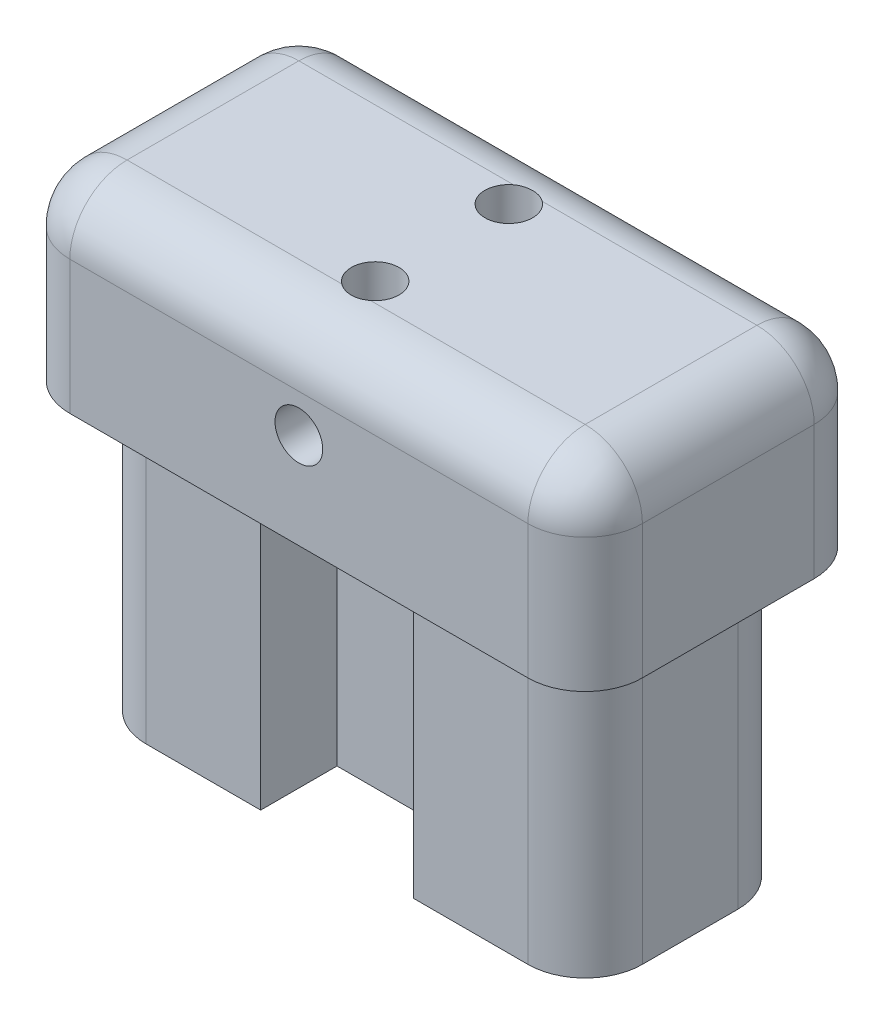
SolidWorks part; units mm, degrees
ref_plane "Front Plane" through (0, 0, 0) normal (0, 0, 1) x (1, 0, 0)
ref_plane "Top Plane" through (0, 0, 0) normal (0, 1, 0) x (1, 0, 0)
ref_plane "Right Plane" through (0, 0, 0) normal (1, 0, 0) x (0, 0, -1)
sketch "Sketch1" plane through (0, 0, 0) normal (0, 1, 0) x (1, 0, 0)
  line L1 (-15, -7.5) -> (15, -7.5)
  line L2 (-15, -7.5) -> (-15, 7.5)
  line L3 (-15, 7.5) -> (15, 7.5)
  line L4 (15, -7.5) -> (15, 7.5)
  line L5 (-15, -7.5) -> (15, 7.5) construction
  line L6 (-15, 7.5) -> (15, -7.5) construction
  point P0 (0, 0)
  dimension "D1" = 30
  dimension "D2" = 15
extrude "Boss-Extrude1" add sketch "Sketch1" along normal blind 10
sketch "Sketch2" plane through (0, 0, 0) normal (0, -1, 0) x (1, 0, 0)
  line L0 (15, 7.5) -> (15, -7.5) construction
  line L1 (-13, -5.5) -> (-4, -5.5)
  line L2 (-13, -5.5) -> (-13, 5.5)
  line L3 (-13, 5.5) -> (-4, 5.5)
  line L4 (13, -5.5) -> (13, 5.5)
  line L5 (-13, -5.5) -> (13, 5.5) construction
  line L6 (-13, 5.5) -> (13, -5.5) construction
  line L7 (-15, 7.5) -> (15, 7.5) construction
  line L8 (-4, 5.5) -> (-4, 1.5)
  line L9 (-4, 1.5) -> (4, 1.5)
  line L10 (4, 1.5) -> (4, 5.5)
  line L11 (4, 5.5) -> (13, 5.5)
  line L12 (-4, -5.5) -> (-4, -1.5)
  line L13 (-4, -1.5) -> (4, -1.5)
  line L14 (4, -1.5) -> (4, -5.5)
  line L15 (4, -5.5) -> (13, -5.5)
  point P0 (0, 0)
  dimension "D1" = 2
  dimension "D2" = 2
  dimension "D3" = 4
  dimension "D4" = 4
  dimension "D5" = 4
  dimension "D6" = 8
  dimension "D7" = 8
extrude "Boss-Extrude2" add sketch "Sketch2" along normal blind 15
fillet "Fillet1" radius 3 12 edges at (-15, 10, 0) (15, 10, 0) (0, 10, -7.5) (0, 10, 7.5) (15, 5, -7.5) (15, 5, 7.5) (-15, 5, -7.5) (-15, 5, 7.5) (13, -7.5, -5.5) (13, -7.5, 5.5) (-13, -7.5, -5.5) (-13, -7.5, 5.5)
sketch "Sketch3" plane through (0, 0, 0) normal (0, -1, 0) x (1, 0, 0)
  line L0 (-4, -1.5) -> (4, -1.5) construction
  line L1 (4, 1.5) -> (-4, 1.5) construction
  circle A0 centre (0, 3.5) radius 1.25
  circle A1 centre (0, -3.5) radius 1.25
  dimension "D1" = 2.5
  dimension "D2" = 2.5
  dimension "D3" = 2
  dimension "D4" = 2
extrude "Cut-Extrude1" cut sketch "Sketch3" against normal through all
sketch "Sketch4" plane through (0, 0, 7.5) normal (0, 0, 1) x (1, 0, 0)
  line L0 (-12, 0) -> (12, 0) construction
  circle A0 centre (0, 5) radius 1.25
  dimension "D1" = 2.5
  dimension "D2" = 5
extrude "Cut-Extrude2" cut sketch "Sketch4" against normal through all
